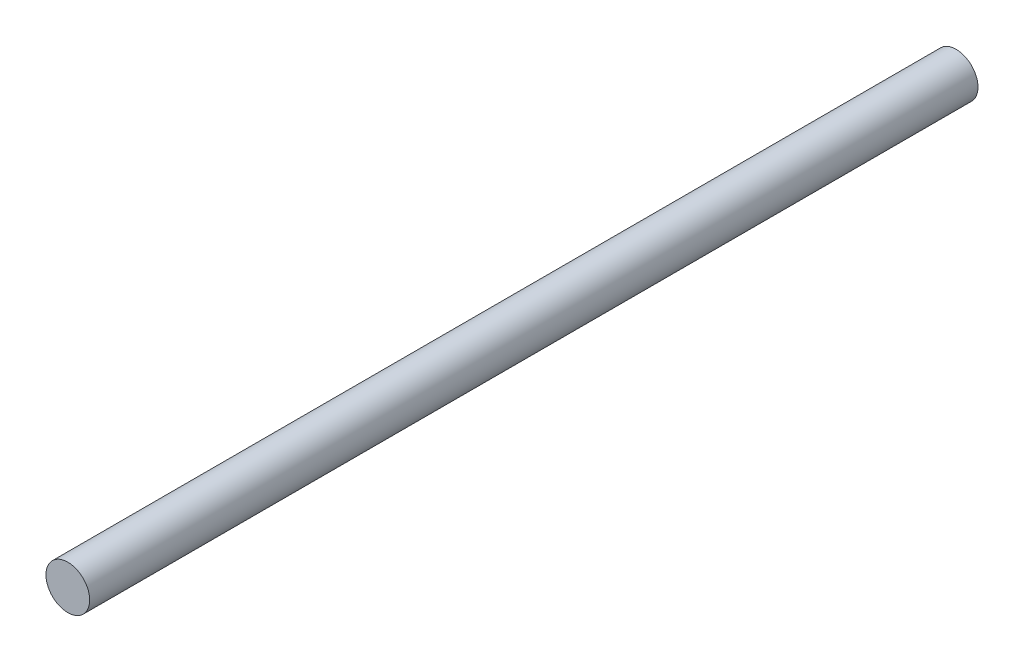
SolidWorks part; units mm, degrees
ref_plane "Front" through (0, 0, 0) normal (0, 0, 1) x (1, 0, 0)
ref_plane "Top" through (0, 0, 0) normal (0, 1, 0) x (1, 0, 0)
ref_plane "Right" through (0, 0, 0) normal (1, 0, 0) x (0, 0, -1)
sketch "Sketch1" plane through (0, 0, 0) normal (0, 0, 1) x (1, 0, 0)
  circle A0 centre (0, 0) radius 8
  dimension "D1" = 16
extrude "Boss-Extrude1" add sketch "Sketch1" along normal mid plane 325
